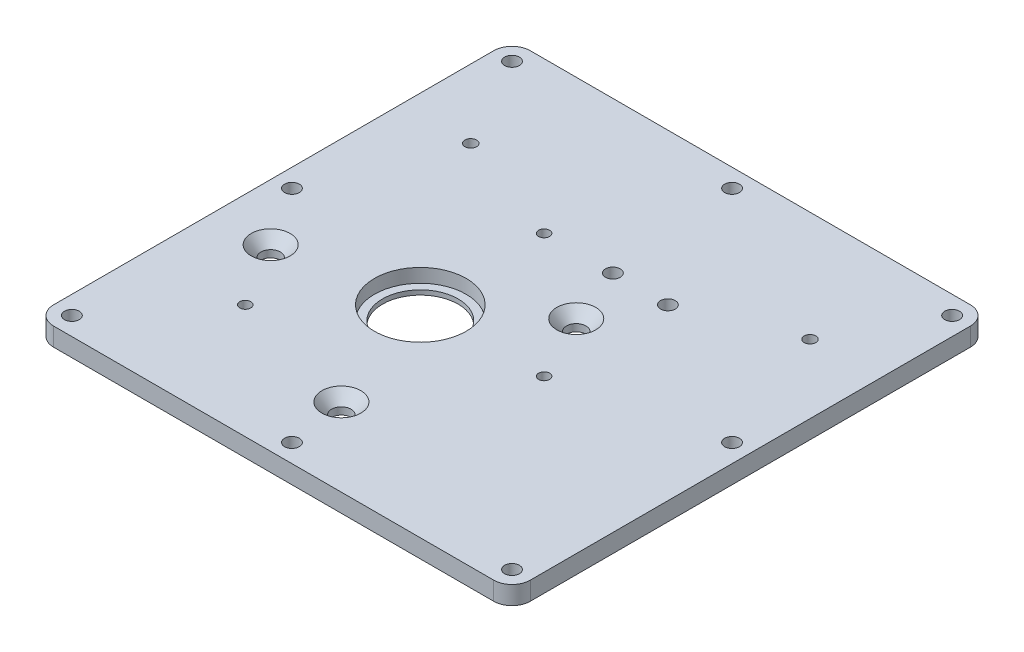
SolidWorks part; units mm, degrees
material "5052-H32"
ref_plane "Front Plane" through (0, 0, 0) normal (0, 0, 1) x (1, 0, 0)
ref_plane "Top Plane" through (0, 0, 0) normal (0, 1, 0) x (1, 0, 0)
ref_plane "Right Plane" through (0, 0, 0) normal (1, 0, 0) x (0, 0, -1)
sketch "Sketch1" plane through (0, 0, 0) normal (0, 1, 0) x (1, 0, 0)
  line L1 (82.55, -82.55) -> (-82.55, -82.55)
  line L2 (82.55, -82.55) -> (82.55, 82.55)
  line L3 (82.55, 82.55) -> (-82.55, 82.55)
  line L4 (-82.55, -82.55) -> (-82.55, 82.55)
  line L5 (82.55, -82.55) -> (-82.55, 82.55) construction
  line L6 (82.55, 82.55) -> (-82.55, -82.55) construction
  circle A0 centre (-19.05, -12.7) radius 13.0969
  circle A1 centre (23.8125, -12.7) radius 1.5875
  point P0 (0, 0)
  dimension "D5" = 26.1937
  dimension "D6" = 3.175
  dimension "D1" = 165.1
  dimension "D2" = 165.1
  dimension "D3" = 42.8625
  dimension "D4" = 63.5
  dimension "D7" = 69.85
extrude "Boss-Extrude1" add sketch "Sketch1" along normal blind 6.35
sketch "Sketch3" plane through (0, 6.35, 0) normal (0, -1, 0) x (1, 0, 0)
  circle A0 centre (-19.05, 12.7) radius 15.875
  dimension "D1" = 31.75
extrude "Cut-Extrude1" cut sketch "Sketch3" along normal blind 4.7625
sketch "Sketch6" plane through (0, 6.35, 0) normal (0, 1, 0) x (1, 0, 0)
  circle A0 centre (-3.6068, -55.4736) radius 3.175
  circle A1 centre (-62.992, -20.574) radius 3.175
  circle A2 centre (12.0904, 10.16) radius 3.175
  circle A5 centre (-19.05, -12.7) radius 15.875 construction
  circle A6 centre (-19.05, -12.7) radius 15.875
  dimension "D3" = 6.35
  dimension "D1" = 15.4432
  dimension "D2" = 42.7736
  dimension "D4" = 7.874
  dimension "D5" = 43.942
  dimension "D6" = 22.86
  dimension "D7" = 31.1404
hole_wizard "CSK for 1/4 Flat Head Socket Cap Screw1" positions "Sketch7" profile "Sketch8" countersink size "1/4" standard "ANSI Inch" end condition through all
sketch "Sketch7" plane through (0, 6.35, 0) normal (0, 1, 0) x (1, 0, 0)
  point P0 (-62.992, -20.574)
  point P3 (12.0904, 10.16)
  point P6 (-3.6068, -55.4736)
sketch "Sketch8" plane through (-62.992, 6.35, 20.574) normal (1, 0, 0) x (0, 0, 1)
  line L0 (0, 0) -> (0, 6.35)
  line L1 (0, 6.35) -> (3.3782, 6.35)
  line L2 (3.3782, 6.35) -> (3.3782, 3.8716)
  line L3 (3.3782, 3.8716) -> (6.7437, 0)
  line L5 (6.7437, 0) -> (0, 0)
  line L6 (-3.3782, 3.8716) -> (-6.7437, 0) construction
  line L11 (0, -6.35) -> (0, 107.95) construction
  dimension "Thru Hole Dia." = 6.7564
  dimension "Thru Hole Depth" = 6.35
  dimension "Near C'Sink Dia." = 13.4874
  dimension "Near C'Sink Angle" = 82
fillet "Fillet1" radius 6.35 4 edges at (82.55, 3.175, -82.55) (82.55, 3.175, 82.55) (-82.55, 3.175, 82.55) (-82.55, 3.175, -82.55)
hole_wizard "#10 Clearance Hole1" positions "Sketch9" profile "Sketch10" hole size "#10" standard "ANSI Inch" end condition through all
sketch "Sketch9" plane through (0, 6.35, 0) normal (0, 1, 0) x (1, 0, 0)
  line L0 (-76.2, 76.2) -> (76.2, 76.2)
  line L1 (76.2, 76.2) -> (76.2, -76.2)
  line L2 (76.2, -76.2) -> (-76.2, -76.2)
  line L3 (-76.2, -76.2) -> (-76.2, 76.2)
  point P0 (-76.2, -76.2)
  point P3 (-76.2, 76.2)
  point P6 (76.2, 76.2)
  point P9 (76.2, -76.2)
  point P21 (0, 76.2)
  point P23 (0, -76.2)
  point P32 (-76.2, 0)
  point P36 (76.2, 0)
sketch "Sketch10" plane through (-76.2, 6.35, 76.2) normal (1, 0, 0) x (0, 0, 1)
  line L0 (0, 0) -> (0, 6.35)
  line L1 (0, 6.35) -> (2.5527, 6.35)
  line L2 (2.5527, 6.35) -> (2.5527, 0)
  line L5 (2.5527, 0) -> (0, 0)
  line L11 (0, -6.35) -> (0, 107.95) construction
  dimension "Thru Hole Dia." = 5.1054
  dimension "Thru Hole Depth" = 6.35
hole_wizard "#10-24 Tapped Hole1" positions "Sketch11" profile "Sketch13" tap size "#10-24" standard "ANSI Inch"
sketch "Sketch11" plane through (0, 6.35, 0) normal (0, 1, 0) x (1, 0, 0)
  circle A1 centre (-19.05, -12.7) radius 13.0969 construction
  circle A2 centre (-19.05, -12.7) radius 42.8625 construction
  point P0 (23.8125, -12.7)
  point P12 (-49.3584, -43.0084)
  point P13 (-19.05, 30.1625)
  point P14 (-19.05, -12.7)
  dimension "D1" = 90
  dimension "D2" = 135
sketch "Sketch13" plane through (23.8125, 6.35, 12.7) normal (1, 0, 0) x (0, 0, 1)
  line L0 (0, 0) -> (0, 17.1428)
  line L1 (0, 17.1428) -> (1.8986, 16.002)
  line L2 (1.8986, 16.002) -> (1.8986, 0)
  line L5 (1.8986, 0) -> (0, 0)
  line L10 (0, 17.1428) -> (-1.8987, 16.002) construction
  line L11 (0, -6.35) -> (0, 107.95) construction
  dimension "Tap Drill Dia." = 3.7973
  dimension "Tap Drill Depth" = 16.002
  dimension "Drill Angle" = 118
hole_wizard "#10 Clearance Hole2" positions "Sketch14" profile "Sketch15" hole size "#10" standard "ANSI Inch" end condition through all
sketch "Sketch14" plane through (0, 6.35, 0) normal (0, 1, 0) x (1, 0, 0)
  line L0 (23.8125, -12.7) -> (23.8125, 30.1625) construction
  line L1 (23.8125, 30.1625) -> (-19.05, 30.1625) construction
  point P0 (23.8125, 30.1625)
  point P17 (4.7625, 30.1625)
  dimension "D4" = 19.05
sketch "Sketch15" plane through (23.8125, 6.35, -30.1625) normal (1, 0, 0) x (0, 0, 1)
  line L0 (0, 0) -> (0, 6.35)
  line L1 (0, 6.35) -> (2.5527, 6.35)
  line L2 (2.5527, 6.35) -> (2.5527, 0)
  line L5 (2.5527, 0) -> (0, 0)
  line L11 (0, -6.35) -> (0, 107.95) construction
  dimension "Thru Hole Dia." = 5.1054
  dimension "Thru Hole Depth" = 6.35
sketch "Sketch16" plane through (0, 0, 0) normal (0, -1, 0) x (1, 0, 0)
  line L0 (-76.2, 82.55) -> (76.2, 82.55) construction
  line L1 (69.85, -69.85) -> (-69.85, -69.85)
  line L2 (69.85, -69.85) -> (69.85, 69.85)
  line L3 (69.85, 69.85) -> (-69.85, 69.85)
  line L4 (-69.85, -69.85) -> (-69.85, 13.6743)
  line L5 (69.85, -69.85) -> (-69.85, 69.85) construction
  line L6 (69.85, 69.85) -> (-69.85, -69.85) construction
  line L7 (82.55, 76.2) -> (82.55, -76.2) construction
  line L8 (-69.85, 27.4737) -> (-69.85, 69.85)
  circle A0 centre (-19.05, 12.7) radius 13.0969 construction
  circle A1 centre (-62.992, 20.574) radius 3.3782 construction
  circle A2 centre (-49.3584, 43.0084) radius 1.8986 construction
  circle A3 centre (-19.05, -30.1625) radius 1.8986 construction
  circle A4 centre (-3.6068, 55.4736) radius 3.3782 construction
  circle A5 centre (23.8125, 12.7) radius 1.8986 construction
  circle A6 centre (12.0904, -10.16) radius 3.3782 construction
  circle A7 centre (4.7625, -30.1625) radius 2.5527 construction
  circle A8 centre (-49.3584, 43.0084) radius 1.8986
  circle A9 centre (23.8125, -30.1625) radius 2.5527 construction
  circle A10 centre (-19.05, -30.1625) radius 1.8986
  circle A11 centre (-19.05, 12.7) radius 13.0969
  circle A12 centre (-62.992, 20.574) radius 3.3782
  circle A15 centre (-3.6068, 55.4736) radius 3.3782
  circle A16 centre (23.8125, 12.7) radius 1.8986
  circle A17 centre (12.0904, -10.16) radius 3.3782
  circle A18 centre (4.7625, -30.1625) radius 2.5527
  circle A20 centre (23.8125, -30.1625) radius 2.5527
  circle A22 centre (-19.05, 12.7) radius 19.4469
  arc A23 (-69.85, 13.6743) -> (-69.85, 27.4737) centre (-62.992, 20.574) ccw
  circle A26 centre (-3.6068, 55.4736) radius 9.7282
  circle A27 centre (23.8125, 12.7) radius 8.2486
  arc A28 (20.8192, -14.4548) -> (3.7062, -15.0939) centre (12.0904, -10.16) ccw
  arc A29 (1.4003, -21.9191) -> (10.9679, -36.5461) centre (4.7625, -30.1625) ccw
  arc A31 (17.6071, -36.5461) -> (24.6464, -21.2989) centre (23.8125, -30.1625) ccw
  circle A33 centre (-19.05, -30.1625) radius 8.2486
  circle A34 centre (-62.992, 20.574) radius 9.7282 construction
  circle A35 centre (-49.3584, 43.0084) radius 8.2486
  arc A36 (1.4003, -21.9191) -> (3.7062, -15.0939) centre (-0.3983, -17.5093) ccw
  arc A37 (20.8192, -14.4548) -> (24.6464, -21.2989) centre (25.0925, -16.5574) ccw
  arc A38 (17.6071, -36.5461) -> (10.9679, -36.5461) centre (14.2875, -39.9611) ccw
  circle A40 centre (4.7625, -30.1625) radius 8.9027 construction
  circle A41 centre (12.0904, -10.16) radius 9.7282 construction
  circle A42 centre (23.8125, -30.1625) radius 8.9027 construction
  point P4 (0, 0)
  point P25 (-45.6027, 21.8349)
  point P46 (38.3847, -21.9062)
  point P63 (19.3347, -21.9062)
  point P67 (30.6685, -6.2568)
  dimension "D5" = 4.7625
  dimension "D2" = 12.7
  dimension "D3" = 12.7
  dimension "D1" = 6.35
  dimension "D4" = 6.35
extrude "Cut-Extrude2" cut sketch "Sketch16" against normal blind 3.175 contours A23 L4 L1 L2 L3 L8 A31 A29 A28 A27 A26 A22
fillet "Fillet2" radius 3.175 6 edges at (69.85, 1.5875, 69.85) (-69.85, 1.5875, 69.85) (-69.85, 1.5875, 13.6743) (-69.85, 1.5875, 27.4737) (-69.85, 1.5875, -69.85) (69.85, 1.5875, -69.85)
sketch "Sketch17" plane through (0, 6.35, 0) normal (0, 1, 0) x (1, 0, 0)
  line L0 (-19.05, 19.05) -> (82.55, 19.05) construction
  line L1 (82.55, -76.2) -> (82.55, 76.2) construction
  line L2 (42.8713, -2.6726) -> (44.4579, 44.926) construction
  circle A0 centre (58.7375, 44.45) radius 23.8125 construction
  circle A1 centre (-19.05, -12.7) radius 31.75 construction
  circle A2 centre (58.7375, -3.2015) radius 15.875 construction
  circle A3 centre (58.7375, 44.45) radius 14.2875 construction
  circle A4 centre (58.7375, 44.45) radius 22.225 construction
  circle A5 centre (23.8125, 30.1625) radius 2.5527 construction
  dimension "D1" = 34.925
  dimension "D2" = 63.5
  dimension "D3" = 28.575
  dimension "D4" = 31.75
  dimension "D6" = 44.45
  dimension "D5" = 47.625
  dimension "D7" = 25.4
hole_wizard "#10-32 Tapped Hole1" positions "Sketch18" profile "Sketch19" tap size "#10-32" standard "ANSI Inch" end condition through all
sketch "Sketch18" plane through (0, 6.35, 0) normal (0, 1, 0) x (1, 0, 0)
  point P3 (58.7375, 44.45)
  point P8 (-58.7375, 44.45)
  dimension "D1" = 117.475
sketch "Sketch19" plane through (58.7375, 6.35, -44.45) normal (1, 0, 0) x (0, 0, 1)
  line L0 (0, 0) -> (0, 6.35)
  line L1 (0, 6.35) -> (2.0193, 6.35)
  line L2 (2.0193, 6.35) -> (2.0193, 0)
  line L5 (2.0193, 0) -> (0, 0)
  line L11 (0, -6.35) -> (0, 107.95) construction
  dimension "Thru Tap Drill Dia." = 4.0386
  dimension "Thru Tap Drill Depth" = 6.35
cosmetic thread "Hole Thread1" parameters "D2"=4.826
cosmetic thread "Hole Thread2" parameters "D2"=4.826
equation "\"D3@Sketch1\"=2.5/2+.625/2+.125"
equation "\"D4@Sketch16\"=\"D1@Sketch16\""
